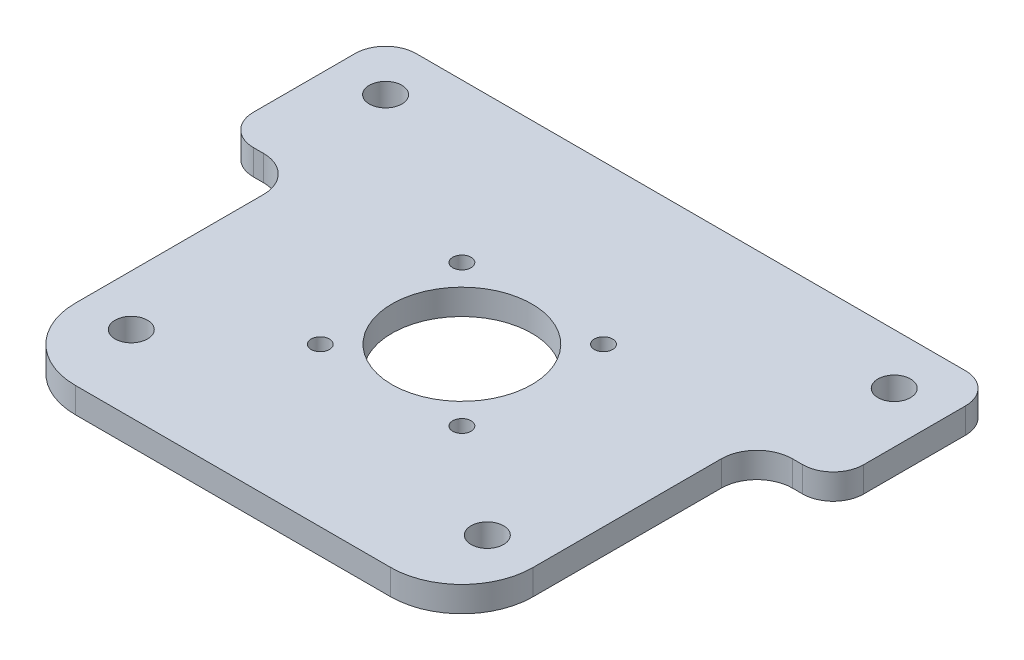
SolidWorks part; units mm, degrees
ref_plane "Front Plane" through (0, 0, 0) normal (0, 0, 1) x (1, 0, 0)
ref_plane "Top Plane" through (0, 0, 0) normal (0, 1, 0) x (1, 0, 0)
ref_plane "Right Plane" through (0, 0, 0) normal (1, 0, 0) x (0, 0, -1)
sketch "Sketch1" plane through (0, 0, 0) normal (0, 1, 0) x (1, 0, 0)
  line L1 (-57.15, 57.15) -> (57.15, 57.15)
  line L2 (-57.15, 57.15) -> (-57.15, -57.15)
  line L3 (-57.15, -57.15) -> (57.15, -57.15)
  line L4 (57.15, 57.15) -> (57.15, -57.15)
  line L5 (-57.15, 57.15) -> (57.15, -57.15) construction
  line L6 (-57.15, -57.15) -> (57.15, 57.15) construction
  point P0 (0, 0)
  dimension "D1" = 114.3
extrude "Boss-Extrude1" add sketch "Sketch1" along normal blind 6.35 contours L1 L4 L3 L2
sketch "Sketch3" plane through (0, 6.35, 0) normal (0, 1, 0) x (1, 0, 0)
  line L1 (57.15, 16.51) -> (76.2, 16.51)
  line L2 (57.15, 16.51) -> (57.15, 57.15)
  line L3 (57.15, 57.15) -> (76.2, 57.15)
  line L4 (76.2, 16.51) -> (76.2, 57.15)
  line L5 (-57.15, 16.51) -> (-76.2, 16.51)
  line L6 (-57.15, 16.51) -> (-57.15, 57.15)
  line L7 (-57.15, 57.15) -> (-76.2, 57.15)
  line L8 (-76.2, 16.51) -> (-76.2, 57.15)
  dimension "D1" = 40.64
  dimension "D2" = 19.05
extrude "Boss-Extrude2" add sketch "Sketch3" against normal up to surface (6.35 mm away) up to face at (0, 0, 0)
sketch "Sketch2" plane through (0, 6.35, 0) normal (0, 1, 0) x (1, 0, 0)
  line L0 (0, 0) -> (0, 17.6777) construction
  line L1 (-63.5, 44.45) -> (63.5, 44.45) construction
  line L3 (-44.45, -38.1) -> (44.45, -38.1) construction
  line L7 (-17.6777, -17.6777) -> (17.6777, -17.6777) construction
  line L8 (-17.6777, -17.6777) -> (-17.6777, 17.6777) construction
  line L9 (-17.6777, 17.6777) -> (17.6777, 17.6777) construction
  line L10 (17.6777, -17.6777) -> (17.6777, 17.6777) construction
  line L11 (-17.6777, -17.6777) -> (17.6777, 17.6777) construction
  line L12 (-17.6777, 17.6777) -> (17.6777, -17.6777) construction
  circle A0 centre (-63.5, 44.45) radius 4.064
  circle A1 centre (63.5, 44.45) radius 4.064
  circle A2 centre (44.45, -38.1) radius 4.064
  circle A3 centre (-44.45, -38.1) radius 4.064
  circle A4 centre (0, 0) radius 17.4625
  circle A5 centre (-17.6777, 17.6777) radius 2.286
  circle A6 centre (17.6777, 17.6777) radius 2.286
  circle A7 centre (17.6777, -17.6777) radius 2.286
  circle A8 centre (-17.6777, -17.6777) radius 2.286
  point P0 (0, 0)
  dimension "D2" = 8.128
  dimension "D3" = 34.925
  dimension "D4" = 4.572
  dimension "D5" = 50
  dimension "D1" = 127
  dimension "D6" = 44.45
  dimension "D7" = 38.1
  dimension "D8" = 88.9
extrude "Cut-Extrude1" cut sketch "Sketch2" against normal through all
fillet "Fillet1" radius 8.89 2 edges
fillet "Fillet2" radius 17.78 2 edges at (-57.15, 3.175, 57.15) (57.15, 3.175, 57.15)
fillet "Fillet3" radius 7.62 4 edges at (76.2, 3.175, -16.51) (76.2, 3.175, -57.15) (-76.2, 3.175, -57.15) (-76.2, 3.175, -16.51)
